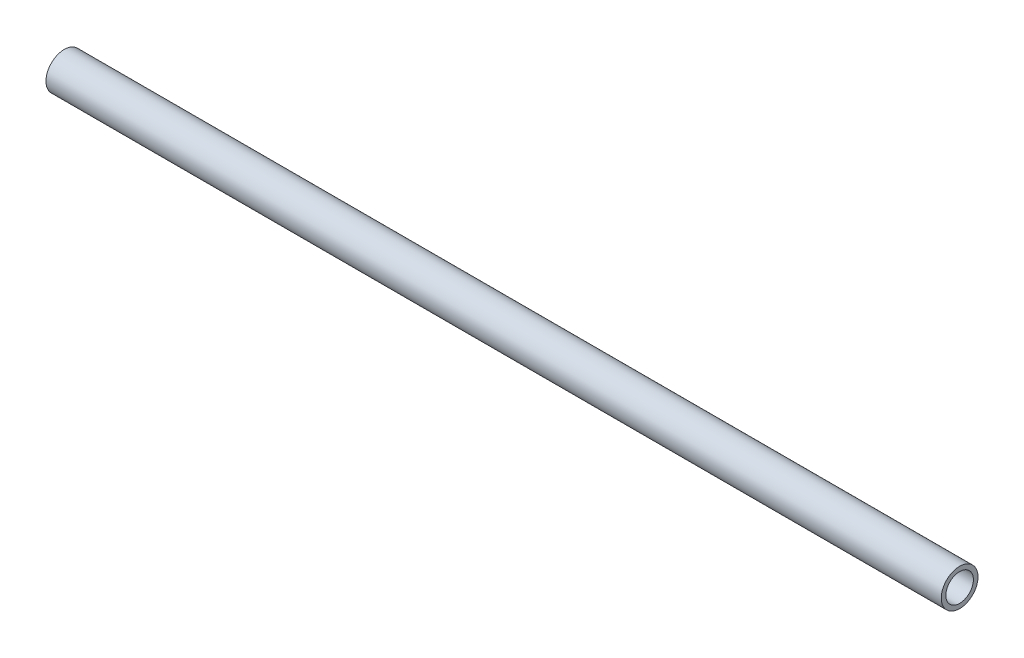
SolidWorks part; units mm, degrees
material "6061-T6 (SS)"
ref_plane "Front Plane" through (0, 0, 0) normal (0, 0, 1) x (1, 0, 0)
ref_plane "Top Plane" through (0, 0, 0) normal (0, 1, 0) x (1, 0, 0)
ref_plane "Right Plane" through (0, 0, 0) normal (1, 0, 0) x (0, 0, -1)
sketch "Sketch1" plane through (0, 0, 0) normal (1, 0, 0) x (0, 0, -1)
  circle A0 centre (0, 0) radius 12.7
  circle A1 centre (0, 0) radius 9.525
  dimension "D1" = 25.4
  dimension "D2" = 3.175
extrude "Boss-Extrude1" add sketch "Sketch1" along normal mid plane 619.125
